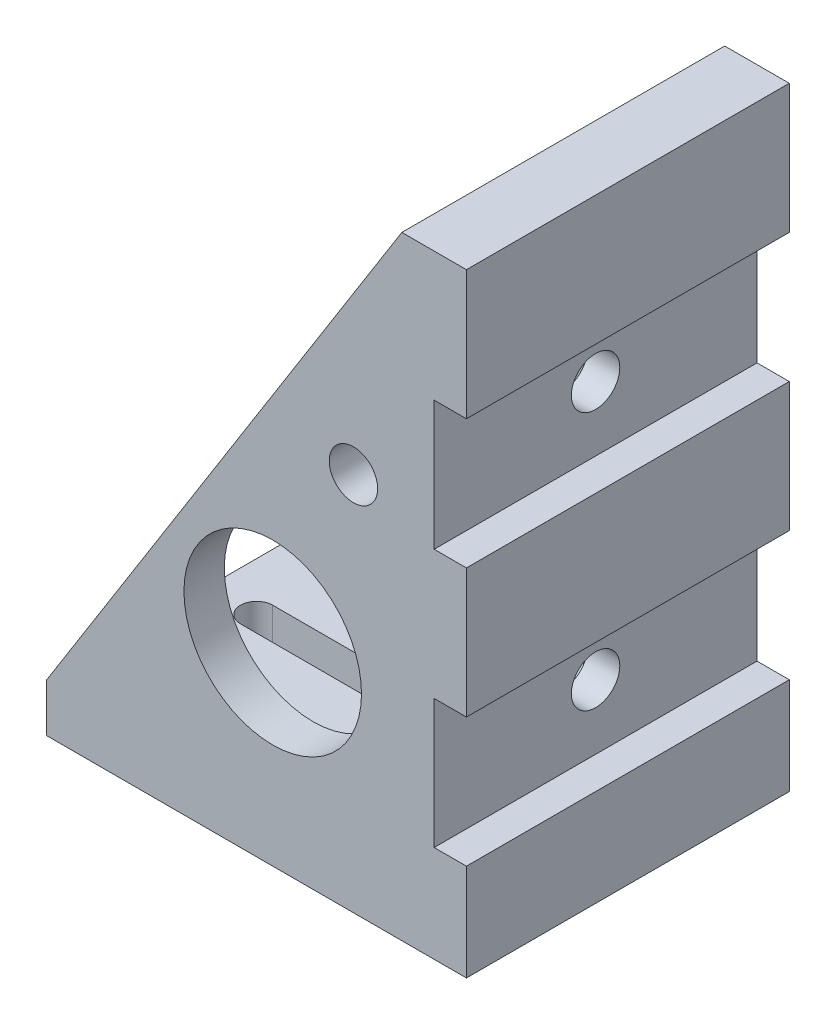
SolidWorks part; units mm, degrees
ref_plane "Front Plane" through (0, 0, 0) normal (0, 0, 1) x (1, 0, 0)
ref_plane "Top Plane" through (0, 0, 0) normal (0, 1, 0) x (1, 0, 0)
ref_plane "Right Plane" through (0, 0, 0) normal (1, 0, 0) x (0, 0, -1)
sketch "Sketch1" plane through (0, 0, 0) normal (0, 0, 1) x (1, 0, 0)
  line L0 (-13, 0) -> (13, 0)
  line L1 (-13, 0) -> (-13, 3)
  line L2 (-13, 3) -> (9, 38)
  line L3 (-13, 3) -> (20.3287, 3) construction
  line L4 (9, 38) -> (13, 38)
  line L5 (13, 0) -> (13, 38)
  point P4 (0, 0)
  dimension "D1" = 26
  dimension "D2" = 3
  dimension "D3" = 38
  dimension "D4" = 4
extrude "Boss-Extrude1" add sketch "Sketch1" along normal blind 20
sketch "Sketch2" plane through (13, 0, 0) normal (1, 0, 0) x (0, 0, -1)
  line L0 (-20, 0) -> (-20, 38) construction
  line L1 (-20, 14) -> (0, 14)
  line L2 (-20, 14) -> (-20, 6)
  line L3 (-20, 6) -> (0, 6)
  line L4 (0, 14) -> (0, 6)
  line L5 (0, 0) -> (0, 38) construction
  line L6 (-20, 0) -> (0, 0) construction
  line L8 (-20, 22) -> (0, 22)
  line L9 (-20, 22) -> (-20, 30)
  line L10 (-20, 30) -> (0, 30)
  line L11 (0, 22) -> (0, 30)
  dimension "D1" = 8
  dimension "D2" = 6
  dimension "D3" = 8
  dimension "D4" = 8
extrude "Cut-Extrude1" cut sketch "Sketch2" against normal blind 2
sketch "Sketch3" plane through (-10.67, 6.7068, 0) normal (-0.8466, 0.5322, 0) x (0, 0, 1)
  line L0 (2.5, 36.9617) -> (2.5, -4.3783)
  line L1 (2.5, -4.3783) -> (17.5, -4.3783)
  line L2 (17.5, -4.3783) -> (17.5, 36.9617)
  line L4 (20, -4.3783) -> (0, -4.3783) construction
  line L5 (2.5, 36.9617) -> (17.5, 36.9617)
  line L6 (20, 36.9617) -> (0, 36.9617) construction
ref_plane "Plane1" through (-13, 0, 0) normal (-1, 0, 0) x (0, 0, 1)
sketch "Sketch4" plane through (-13, 0, 0) normal (-1, 0, 0) x (0, 0, 1)
  line L0 (2.5, 38) -> (2.5, 3) construction
  line L1 (17.5, 3) -> (17.5, 38) construction
  line L2 (2.5, 3) -> (17.5, 3) construction
  line L3 (2.5, 38) -> (17.5, 38) construction
  line L4 (2.5, 38) -> (2.5, 3)
  line L5 (17.5, 3) -> (17.5, 38)
  line L6 (2.5, 3) -> (17.5, 3)
  line L7 (2.5, 38) -> (17.5, 38)
extrude "Cut-Extrude2" cut sketch "Sketch4" against normal up to vertex (22 mm away) up to point (9, 38, 2.5)
sketch "Sketch5" plane through (0, 0, 20) normal (0, 0, 1) x (1, 0, 0)
  line L0 (11, 22) -> (1.0594, 22) construction
  line L1 (11, 30) -> (11, 22) construction
  line L2 (11, 14) -> (11, 6) construction
  line L3 (-13, 0) -> (13, 0) construction
  circle A0 centre (6, 23.5) radius 1.5
  circle A1 centre (1, 12) radius 5.5
  dimension "D1" = 3
  dimension "D3" = 11
  dimension "D2" = 5
  dimension "D4" = 10
  dimension "D5" = 12
extrude "Cut-Extrude3" cut sketch "Sketch5" against normal up to surface (20 mm away) up to face at (8.0769, 17.1538, 0)
sketch "Sketch6" plane through (11, 0, 0) normal (1, 0, 0) x (0, 0, -1)
  line L0 (-20, 26) -> (0, 26) construction
  line L1 (-20, 30) -> (-20, 22) construction
  line L2 (0, 22) -> (0, 30) construction
  line L3 (-20, 10) -> (0, 10) construction
  line L4 (-20, 14) -> (-20, 6) construction
  line L5 (0, 6) -> (0, 14) construction
  circle A0 centre (-10, 26) radius 1.5
  circle A1 centre (-10, 10) radius 1.5
  dimension "D1" = 3
extrude "Cut-Extrude4" cut sketch "Sketch6" against normal up to surface (2 mm away) up to face at (9, 20.5, 10)
sketch "Sketch7" plane through (0, 3, 0) normal (0, 1, 0) x (1, 0, 0)
  line L0 (-13, -10) -> (9, -10) construction
  line L1 (-13, -2.5) -> (-13, -17.5) construction
  line L2 (9, -2.5) -> (9, -17.5) construction
  line L3 (-10, -10) -> (6, -10) construction
  line L4 (-10, -9) -> (6, -9)
  line L5 (-10, -11) -> (6, -11)
  arc A0 (-10, -9) -> (-10, -11) centre (-10, -10) ccw
  arc A1 (6, -11) -> (6, -9) centre (6, -10) ccw
  point P8 (-2, -10)
  dimension "D1" = 1
  dimension "D3" = 3
  dimension "D2" = 3
extrude "Cut-Extrude5" cut sketch "Sketch7" against normal up to surface (3 mm away) up to face at (0, 0, 10)
